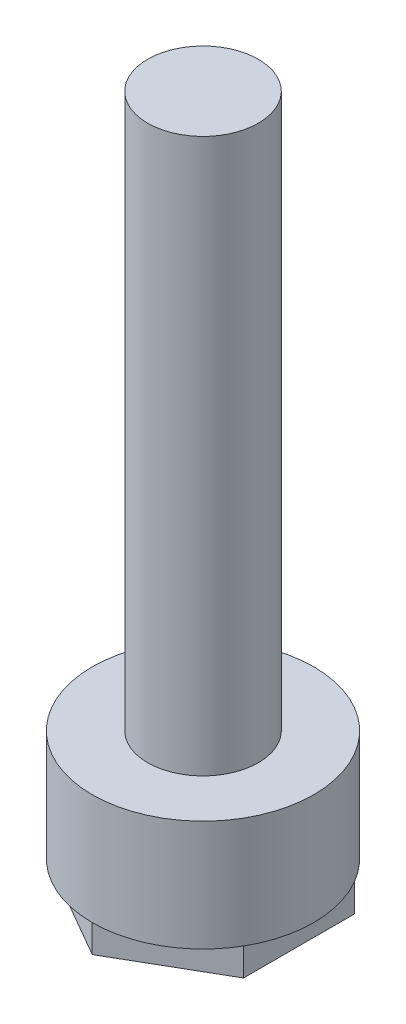
SolidWorks part; units mm, degrees
ref_plane "Front Plane" through (0, 0, 0) normal (0, 0, 1) x (1, 0, 0)
ref_plane "Top Plane" through (0, 0, 0) normal (0, 1, 0) x (1, 0, 0)
ref_plane "Right Plane" through (0, 0, 0) normal (1, 0, 0) x (0, 0, -1)
sketch "Sketch1" plane through (0, 0, 0) normal (0, 1, 0) x (1, 0, 0)
  circle A0 centre (0, 0) radius 2
extrude "Boss-Extrude1" add sketch "Sketch1" along normal blind 2.5
sketch "Sketch2" plane through (0, 2.5, 0) normal (0, 1, 0) x (1, 0, 0)
  circle A0 centre (0, 0) radius 1
extrude "Boss-Extrude2" add sketch "Sketch2" along normal blind 10
sketch "Sketch3" plane through (0, 0, 0) normal (0, -1, 0) x (1, 0, 0)
  line L1 (0, 2) -> (-1.7321, 1)
  line L2 (-1.7321, 1) -> (-1.7321, -1)
  line L3 (-1.7321, -1) -> (0, -2)
  line L4 (0, -2) -> (1.7321, -1)
  line L5 (1.7321, -1) -> (1.7321, 1)
  line L6 (1.7321, 1) -> (0, 2)
  circle A1 centre (0, 0) radius 2 construction
  circle A2 centre (0, 0) radius 2
  circle M7 centre (0, 0) radius 2
extrude "Cut-Extrude3" cut sketch "Sketch3" against normal blind 0.5 contours L1 M7 | L2 M7 | L3 M7 | L4 M7 | L5 M7 | L6 M7
